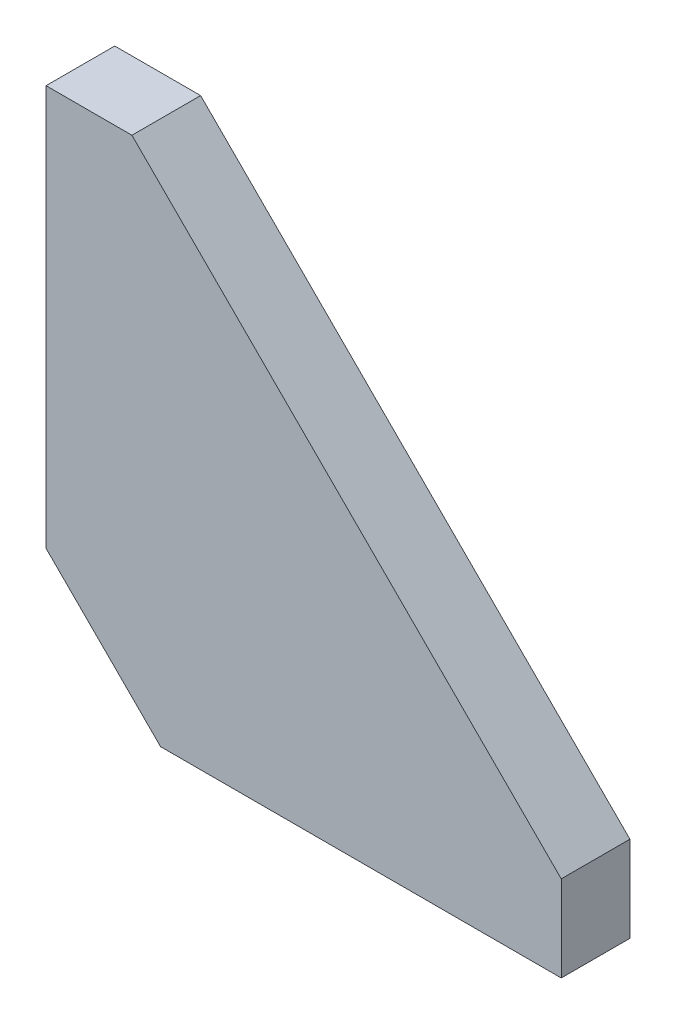
SolidWorks part; units mm, degrees
material "Plain Carbon Steel"
ref_plane "Front Plane" through (0, 0, 0) normal (0, 0, 1) x (1, 0, 0)
ref_plane "Top Plane" through (0, 0, 0) normal (0, 1, 0) x (1, 0, 0)
ref_plane "Right Plane" through (0, 0, 0) normal (1, 0, 0) x (0, 0, -1)
sketch "Sketch1" plane through (0, 0, 0) normal (0, 0, 1) x (1, 0, 0)
  line L0 (-20, 20) -> (-20, 90)
  line L1 (-20, 90) -> (-5, 90)
  line L2 (-5, 90) -> (70, 15)
  line L3 (70, 15) -> (70, 0)
  line L4 (70, 0) -> (0, 0)
  line L5 (-20, 20) -> (0, 0)
  dimension "D1" = 90
  dimension "D2" = 90
  dimension "D3" = 15
  dimension "D4" = 135
  dimension "D5" = 20
extrude "Boss-Extrude1" add sketch "Sketch1" along normal blind 12
